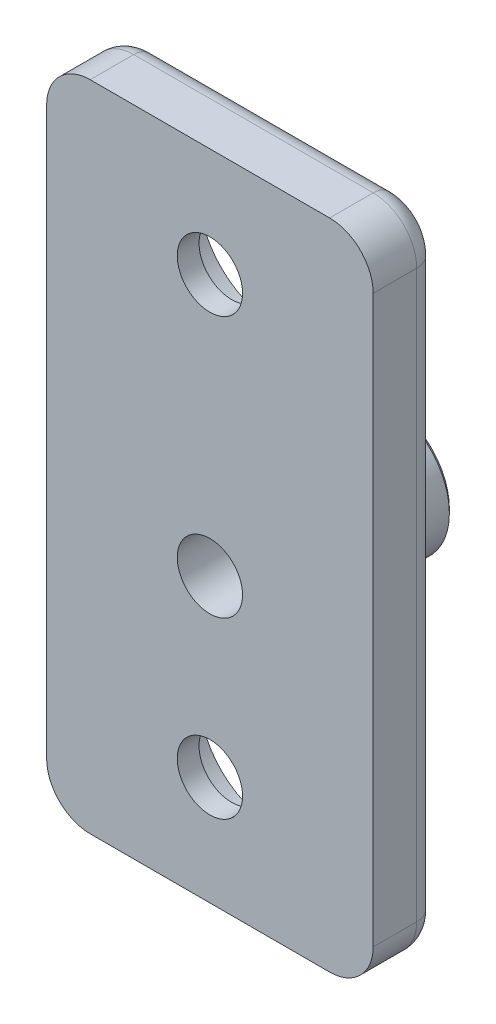
SolidWorks part; units mm, degrees
ref_plane "Front" through (0, 0, 0) normal (0, 0, 1) x (1, 0, 0)
ref_plane "Top" through (0, 0, 0) normal (0, 1, 0) x (1, 0, 0)
ref_plane "Right" through (0, 0, 0) normal (1, 0, 0) x (0, 0, -1)
sketch "Esquisse1" plane through (0, 0, 0) normal (0, 0, 1) x (1, 0, 0)
  line L1 (0, 0) -> (15, 0)
  line L2 (0, 0) -> (0, 30)
  line L3 (0, 30) -> (15, 30)
  line L4 (15, 0) -> (15, 30)
  dimension "D1" = 30
  dimension "D2" = 15
extrude "Boss.-Extru.1" add sketch "Esquisse1" along normal blind 3
sketch "Esquisse2" plane through (0, 0, 0) normal (0, 0, 1) x (1, 0, 0)
  line L0 (7.5, 25.3203) -> (7.5, -10.9238) construction
  line L1 (0, 0) -> (15, 0) construction
  line L2 (15, 0) -> (15, 30) construction
  line L3 (0, 30) -> (0, 0) construction
  circle A0 centre (7.5, 25) radius 1.5
  circle A1 centre (7.5, 5) radius 1.5
  point P6 (0, 0)
  point P7 (0, 0)
  dimension "D3" = 3
  dimension "D1" = 20
  dimension "D2" = 5
extrude "Enlèv. mat.-Extru.2" cut sketch "Esquisse2" along normal blind 3
sketch "Esquisse3" plane through (0, 0, 0) normal (0, 0, 1) x (1, 0, 0)
  circle A0 centre (7.5, 25) radius 3.5
  circle A1 centre (7.5, 5) radius 3.5
  dimension "D1" = 7
extrude "Enlèv. mat.-Extru.3" cut sketch "Esquisse3" along normal blind 2
sketch "Esquisse4" plane through (0, 0, 0) normal (0, 0, 1) x (1, 0, 0)
  line L0 (0, 30) -> (0, 0) construction
  line L1 (0, 0) -> (15, 0) construction
  circle A0 centre (7.5, 13) radius 3
  point P6 (12.3215, 1.9459)
  dimension "D3" = 6
  dimension "D1" = 7.5
  dimension "D2" = 13
extrude "Boss.-Extru.2" add sketch "Esquisse4" against normal blind 5.2
fillet "Congé3" radius 2 4 edges at (15, 30, 1.5) (15, 0, 1.5) (0, 0, 1.5) (0, 30, 1.5)
fillet "Congé4" radius 1 8 edges at (14.4142, 0.5858, 0) (7.5, 0, 0) (0.5858, 0.5858, 0) (0, 15, 0) (0.5858, 29.4142, 0) (7.5, 30, 0) (14.4142, 29.4142, 0) (15, 15, 0)
sketch "Esquisse5" plane through (0, 0, 0) normal (0, 0, 1) x (1, 0, 0)
  circle A0 centre (7.5, 13) radius 1.5
  dimension "D1" = 3
extrude "Enlèv. mat.-Extru.4" cut sketch "Esquisse5" against normal blind 18 and the other way blind 18
chamfer "Chanfrein2" distance 0.2 angle 45 1 edges at (10.5, 13, -5.2)
